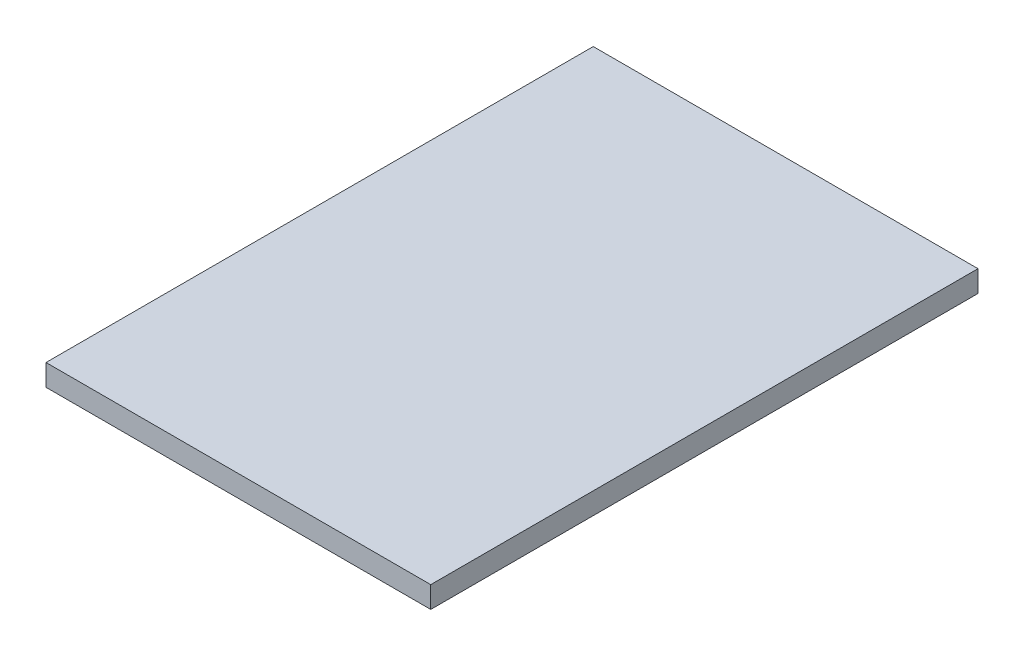
SolidWorks part; units mm, degrees
material "Perspex (TM) GS Acrylic Cast Sheet"
ref_plane "Front Plane" through (0, 0, 0) normal (0, 0, 1) x (1, 0, 0)
ref_plane "Top Plane" through (0, 0, 0) normal (0, 1, 0) x (1, 0, 0)
ref_plane "Right Plane" through (0, 0, 0) normal (1, 0, 0) x (0, 0, -1)
sketch "Sketch1" plane through (0, 0, 0) normal (0, 1, 0) x (1, 0, 0)
  line L1 (-80.5, -114.5) -> (80.5, -114.5)
  line L2 (-80.5, -114.5) -> (-80.5, 114.5)
  line L3 (-80.5, 114.5) -> (80.5, 114.5)
  line L4 (80.5, -114.5) -> (80.5, 114.5)
  line L5 (-80.5, -114.5) -> (80.5, 114.5) construction
  line L6 (-80.5, 114.5) -> (80.5, -114.5) construction
  point P0 (0, 0)
  dimension "D2" = 229
  dimension "D1" = 161
extrude "Boss-Extrude1" add sketch "Sketch1" along normal blind 9
equation "\"PCLength\"= 143mm'Length across I/O from PS to GPU"
equation "\"PCWidth\"= 340mm'Distance of longest part parallel to GPU(ussually GPU)"
equation "\"PCHeight\"= 190mm'Tallest point with mobo laying flat"
equation "\"WallThickness\"= 9mm'Thickness of each outer tank wall"
equation "\"ThermoBarrierThickness\"= 6mm'Thickness of barrier between hot side and cold side"
equation "\"HotSideGap\"= 15mm'Space in the hot side that hot fluid flows into"
equation "\"PCClearance\"= 40mm'Clearance from top of tank to top of PC"
equation "\"RadiatorHeight\"= 277.37mm'Final Height from ground of radiators"
equation "\"D2@Sketch1\"=\"PCHeight\" + \"ThermoBarrierThickness\" + \"HotSideGap\" + (2 * \"WallThickness\") "
equation "\"D1@Boss-Extrude1\"=\"WallThickness\""
equation "\"D1@Sketch1\"=\"PCLength\" + (2 * \"WallThickness\")"
equation "\"AirflowGap\"= 26mm'Distance between radiators and tank for airflow"
equation "\"VolumeSubtraction\"= 230mm"
